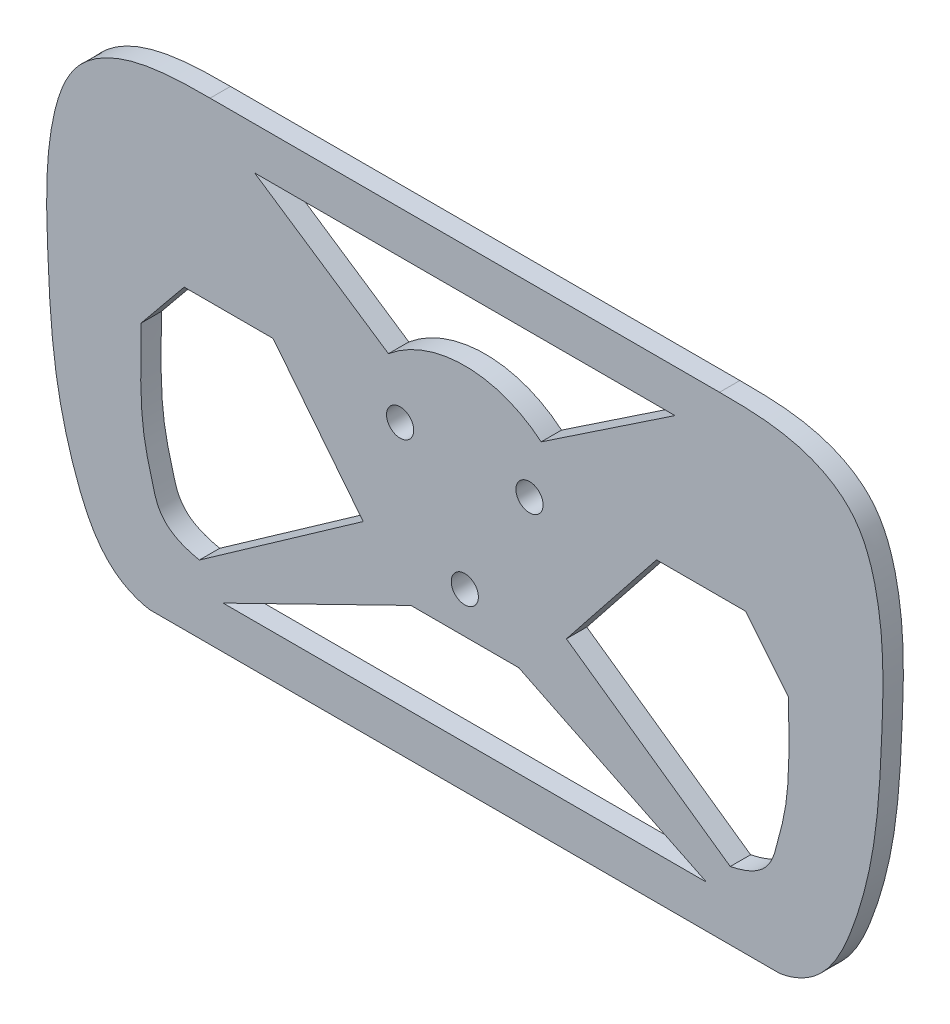
SolidWorks part; units mm, degrees
ref_plane "Front Plane" through (0, 0, 0) normal (0, 0, 1) x (1, 0, 0)
ref_plane "Top Plane" through (0, 0, 0) normal (0, 1, 0) x (1, 0, 0)
ref_plane "Right Plane" through (0, 0, 0) normal (1, 0, 0) x (0, 0, -1)
sketch "Sketch2" plane through (0, 0, 0) normal (0, 0, 1) x (1, 0, 0)
  line L0 (-37.2099, 73.2438) -> (312.1235, 73.2438) construction
sketch "Sketch1" plane through (0, 0, 0) normal (0, 0, 1) x (1, 0, 0)
  line L0 (0, 0) -> (0, 4.7682) construction
  line L2 (-19.05, 10.9985) -> (0, -21.997) construction
  line L3 (0, -21.997) -> (19.05, 10.9985) construction
  line L4 (19.05, 10.9985) -> (-19.05, 10.9985) construction
  line L18 (69.37, 29.9778) -> (95.3562, -1.8435)
  line L19 (92.8419, -73.6201) -> (-92.8419, -73.6201)
  line L21 (69.37, 29.9778) -> (29.9134, -19.6935)
  line L24 (-15.8757, -34.0718) -> (15.8757, -34.0718)
  line L25 (15.8757, -34.0718) -> (71.1705, -61.1201)
  line L26 (71.1705, -61.1201) -> (-71.1705, -61.1201)
  line L29 (-125, 75) -> (125, 75) construction
  line L30 (-125, 75) -> (-125, -75) construction
  line L31 (-125, -75) -> (125, -75) construction
  line L32 (125, 75) -> (125, -75) construction
  line L41 (-15.8757, -34.0718) -> (-71.1705, -61.1201)
  line L42 (-69.37, 29.9778) -> (-95.3562, -1.8435)
  line L45 (-69.37, 29.9778) -> (-29.9134, -19.6935)
  line L46 (78.1549, -53.6301) -> (29.9134, -19.6935)
  line L48 (-78.1549, -53.6301) -> (-29.9134, -19.6935)
  line L50 (22.4848, 26.8222) -> (61.8929, 53.226)
  line L51 (61.8929, 53.226) -> (-61.8929, 53.226)
  line L54 (-22.4848, 26.8222) -> (-61.8929, 53.226)
  line L55 (82.6455, 13.7213) -> (56.4567, 13.7213)
  line L56 (-82.6455, 13.7213) -> (-56.4567, 13.7213)
  line L58 (-75, 65.726) -> (75, 65.726)
  circle A2 centre (-19.05, 10.9985) radius 4
  circle A3 centre (19.05, 10.9985) radius 4
  circle A4 centre (0, -21.997) radius 4
  circle A5 centre (0, 0) radius 21.997 construction
  circle A8 centre (0, 0) radius 35 construction
  arc A9 (22.4848, 26.8222) -> (-22.4848, 26.8222) centre (0, 0) ccw
  spline S0 degree 3 poles (95.3562, -1.8435) (95.5576, -16.5591) (95.606, -27.3438) (91.3094, -43.4531) (89.2123, -51.3576) (78.1549, -53.6301) knots 0 0 0 0 0.501053 0.67815 1 1 1 1
  spline S1 degree 3 poles (75, 65.726) (83.1082, 65.726) (98.0765, 65.5654) (116.2275, 54.9351) (123.7823, 31.9874) (122.9749, 4.1693) (121.473, -25.8179) (114.3636, -53.8816) (105.2223, -71.4115) (92.8419, -73.6201) knots 0 0 0 0 0.144554 0.228464 0.330264 0.520751 0.690485 0.822627 1 1 1 1
  spline S2 degree 3 poles (-95.3562, -1.8435) (-95.5576, -16.5591) (-95.606, -27.3438) (-91.3094, -43.4531) (-89.2123, -51.3576) (-78.1549, -53.6301) knots 0 0 0 0 0.501053 0.67815 1 1 1 1
  spline S5 degree 3 poles (-75, 65.726) (-83.1082, 65.726) (-98.0765, 65.5654) (-116.2275, 54.9351) (-123.7823, 31.9874) (-122.9749, 4.1693) (-121.473, -25.8179) (-114.3636, -53.8816) (-105.2223, -71.4115) (-92.8419, -73.6201) knots 0 0 0 0 0.144554 0.228464 0.330264 0.520751 0.690485 0.822627 1 1 1 1
  point P16 (0, 0)
  point P22 (0, -73.6201)
  point P34 (125, 0)
  point P36 (0, 75)
  point P52 (0, 53.226)
  point P65 (61.8929, 53.226)
  point P70 (0, -61.1201)
  point P71 (0, -34.0718)
  dimension "D1" = 250
  dimension "D2" = 8
  dimension "D3" = 38.1
  dimension "D5" = 12.5
  dimension "D8" = 70
  dimension "D4" = 150
  dimension "D6" = 12.5
extrude "Boss-Extrude1" add sketch "Sketch1" along normal blind 6 contours L58 S5 L19 S1 L18 S0 L46 L21 L50 A9 L54 L51 L41 L24 L25 L26 A2 A3 A4 S2 L42 L45 L48 | L42 L56 L45 | L55 L18 L21
